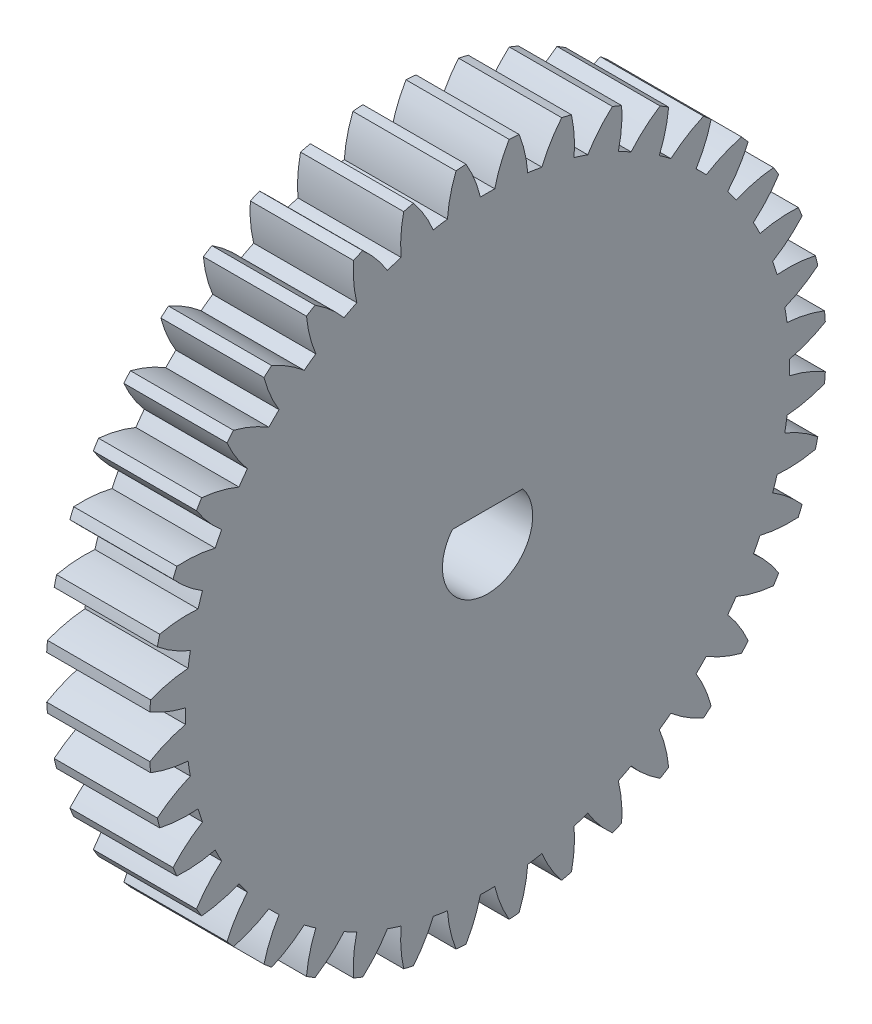
SolidWorks part; units mm, degrees
ref_plane "Plane1" through (0, 0, 0) normal (0, 0, 1) x (1, 0, 0)
ref_plane "Plane2" through (0, 0, 0) normal (0, 1, 0) x (1, 0, 0)
ref_plane "Plane3" through (0, 0, 0) normal (1, 0, 0) x (0, 0, -1)
sketch "HoldingSke" plane through (0, 0, 0) normal (0, 1, 0) x (1, 0, 0)
  line L0 (0, 0) -> (0.6128, -0.5142)
  line L1 (-15, 0) -> (100, 0) construction
  line L2 (0, 0) -> (-2.1039, 2.3779)
  line L3 (0, 0) -> (-11.863, 4.5341)
  line L4 (0, 0) -> (6.6156, 5.5511)
  line L5 (0, 0) -> (-46.8476, -17.4728)
  line L6 (0, 0) -> (-6.6317, -4.4744)
  line L7 (-2.1039, 2.3779) -> (8.6586, 51.2059)
  line L8 (-76.2, 54.61) -> (-75.2, 54.61)
  line L9 (-71.009, 38.7566) -> (-53.1078, 45.2721)
  line L10 (-76.2, 71.12) -> (104.1128, 71.12)
  line L11 (0, 0) -> (-8, 0)
  line L12 (-76.2, 101.6) -> (-76.155, 101.6)
  line L13 (24.9733, 27.94) -> (52.9518, 28.4284)
  line L14 (24.9733, 27.94) -> (24.9743, 27.94)
  line L15 (24.9733, 27.94) -> (100.4006, 29.5858)
  line L16 (-63.627, -1.25) -> (-12.827, -1.25)
  circle A0 centre (0, 0) radius 3.5
  circle A1 centre (0, 0) radius 23.4365
  circle A2 centre (0, 0) radius 37.5
  circle A3 centre (0, 0) radius 3.5
  dimension "MHD" = 46.873
  dimension "Hub_dia" = 75
  dimension "Bore" = 7
  dimension "MBD" = 7
  dimension "Num_teeth" = 40
  dimension "Pitch" = 0.8
  dimension "Overall_len" = 50
  dimension "Show_teeth" = 40
  dimension "Thickness" = 8
  dimension "OAL" = 50.0001
  dimension "T_dim" = 1
  dimension "Ap" = 20
  dimension "H" = 19.05
  dimension "Pitch_radius" = 180.3128
  dimension "Width" = 8
  dimension "Backlash" = 0.045
  dimension "Addendum_fac" = 1
  dimension "Dedendum_fac" = 1.25
  dimension "Clearance_fac" = 0.25
  dimension "Dedendum_add" = 0.001
  dimension "Module" = 1.25
sketch "BasProSke" plane through (0, 0, 0) normal (0, 1, 0) x (1, 0, 0)
  line L0 (-10, 0) -> (60, 0) construction
  line L1 (0, 0) -> (0, 26.25)
  line L2 (0, 0) -> (8, 0)
  line L3 (8, 0) -> (8, 26.25)
  line L4 (8, 26.25) -> (0, 26.25)
  dimension "Thickness" = 8
  dimension "Diameter" = 52.5
revolve "Base-Revolve" add sketch "BasProSke" angle 360 about L0
sketch "TooCutSke" plane through (0, 0, 0) normal (1, 0, 0) x (0, 0, -1)
  line L1 (0, 0) -> (0, 107) construction
  line L2 (0, 0) -> (-1.0602, 24.9775) construction
  line L3 (0, 0) -> (-3.9204, 49.8134) construction
  line L4 (-1.0602, 24.9775) -> (-1.9602, 24.9067) construction
  arc A0 (0.5568, 23.4299) -> (-0.5568, 23.4299) centre (0, 0) ccw
  arc A1 (1.6852, 26.2213) -> (-1.6852, 26.2213) centre (0, 0) ccw
  circle A2 centre (0, 0) radius 25 construction
  circle A3 centre (0, 0) radius 23.4923 construction
  arc A4 (-0.5568, 23.4299) -> (-1.6852, 26.2213) centre (-10.2865, 21.1205) ccw
  arc A5 (1.6852, 26.2213) -> (0.5568, 23.4299) centre (10.2865, 21.1205) ccw
  dimension "Root_dia" = 46.873
  dimension "Overcut_dia" = 52.5508
  dimension "Pitch_dia" = 50
  dimension "Base_dia" = 46.9846
  dimension "Flank_rad" = 10
  dimension "Half_ang" = 4.5
  dimension "Half_CT" = 0.9027
extrude "ToothCut" cut sketch "TooCutSke" along normal through all
fillet "Breaks" [suppressed] radius 0.025
fillet "RootFillets" [suppressed] radius 0.3135
pattern_circular "TeethCuts" count 40 every 9 about axis through (-10, 0, 0) along (1, 0, 0) of "ToothCut", "RootFillets", "Breaks"
sketch "HubNeaOneSke" plane through (0, 0, 0) normal (-1, 0, 0) x (0, 0, 1)
  circle A0 centre (0, 0) radius 23.4365
  dimension "Diameter" = 46.873
extrude "HubNearOne" [suppressed] add sketch "HubNeaOneSke" along normal blind 42.0001
sketch "HubNeaBotSke" plane through (0, 0, 0) normal (-1, 0, 0) x (0, 0, 1)
  circle A0 centre (0, 0) radius 23.4365
  dimension "Diameter" = 46.873
extrude "HubNearBoth" [suppressed] add sketch "HubNeaBotSke" along normal blind 21
ref_plane "FarPln" through (8, 0, 0) normal (1, 0, 0) x (0, 0, -1)
sketch "HubFarSke" plane through (8, 0, 0) normal (1, 0, 0) x (0, 0, -1)
  circle A0 centre (0, 0) radius 23.4365
  dimension "Diameter" = 46.873
extrude "HubFar" [suppressed] add sketch "HubFarSke" along normal blind 21
sketch "BorSke" plane through (0, 0, 0) normal (1, 0, 0) x (0, 0, -1)
  circle A0 centre (0, 0) radius 3.5
  dimension "Diameter" = 7
extrude "Bore" cut sketch "BorSke" along normal mid plane 100.0001
sketch "KeySke" plane through (0, 0, 0) normal (1, 0, 0) x (0, 0, -1)
  line L0 (-1, 0) -> (-1, 4.5)
  line L1 (-1, 4.5) -> (1, 4.5)
  line L2 (1, 4.5) -> (1, 0)
  line L3 (0, 0) -> (0, 34) construction
  line L4 (-1, 0) -> (1, 0)
  dimension "Offset" = 4.5
  dimension "Width" = 2
extrude "Keyway" [suppressed] cut sketch "KeySke" along normal mid plane 100.0001
pattern_circular "Keyway2" [suppressed] count 2 every 90 about axis through (-10, 0, 0) along (1, 0, 0)
sketch "Sketch1" plane through (8, 0, 0) normal (1, 0, 0) x (0, 0, -1)
  line L0 (-2.7305, 2.1896) -> (2.7305, 2.1896)
  circle A0 centre (0, 0) radius 3.5 construction
  circle A1 centre (0, 0) radius 3.5
  point P5 (0, -3.5)
  dimension "D1" = 5.6896
extrude "Boss-Extrude1" add sketch "Sketch1" against normal up to surface (8 mm away) contours L0 A1
equation "' \"Module@HoldingSke\" = 6.35"
equation "' \"Num_teeth@HoldingSke\" = 12"
equation "' \"Ap@HoldingSke\" =  20"
equation "' \"Ap@HoldingSke\" = 20"
equation "' \"Width@HoldingSke\" = 0.5 * 25.4"
equation "' \"Hub_dia@HoldingSke\"= 1 * 25.4"
equation "' \"Hub_dia@HoldingSke\" = 1 * 25.4"
equation "' \"Overall_len@HoldingSke\" = 1.0 * 25.4"
equation "' \"Bore@HoldingSke\" = 0.75 * 25.4"
equation "' \"T_dim@HoldingSke\" = 0.1 * 25.4"
equation "' \"Width@KeySke\" = 0.25 * 25.4"
equation "' \"Show_teeth@HoldingSke\" = 13"
equation "' \"Backlash@HoldingSke\" = 0.009 * 25.4"
equation "' \"Addendum_fac@HoldingSke\" = 1.0"
equation "' \"Dedendum_fac@HoldingSke\" = 1.25"
equation "' \"Dedendum_add@HoldingSke\" = 0.00005 * 25.4"
equation "' \"Clearance_fac@HoldingSke\" = 0.25"
equation "\"Pitch@HoldingSke\" = 1 / \"Module@HoldingSke\""
equation "\"Overcut_dia@TooCutSke\" = (\"Num_teeth@HoldingSke\" + 2 * \"Addendum_fac@HoldingSke\") / \"Pitch@HoldingSke\" + 0.002 * 25.4"
equation "\"Pitch_dia@TooCutSke\" = \"Num_teeth@HoldingSke\" / \"Pitch@HoldingSke\""
equation "\"Base_dia@TooCutSke\" = \"Num_teeth@HoldingSke\" / \"Pitch@HoldingSke\" * cos((\"Ap@HoldingSke\"  * 3.14159265 / 180))"
equation "\"Root_dia@TooCutSke\" = (\"Num_teeth@HoldingSke\" + 2) / \"Pitch@HoldingSke\" - 2 * (\"Addendum_fac@HoldingSke\" + \"Dedendum_fac@HoldingSke\") / \"Pitch@HoldingSke\" - \"Dedendum_add@HoldingSke\" * 2"
equation "\"Half_ang@TooCutSke\" = 180 / \"Num_teeth@HoldingSke\""
equation "\"Half_CT@TooCutSke\" = \"Num_teeth@HoldingSke\" / \"Pitch@HoldingSke\" * sin((3.14159265 / 2 / \"Num_teeth@HoldingSke\")) / 2 - 7 * \"Backlash@HoldingSke\" / 4"
equation "\"Flank_rad@TooCutSke\" = \"Num_teeth@HoldingSke\" / \"Pitch@HoldingSke\" / 5"
equation "\"Radius@RootFillets\" = \"Clearance_fac@HoldingSke\" / \"Pitch@HoldingSke\" + \"Dedendum_add@HoldingSke\""
equation "\"Break_rad@Breaks\" = 0.02 / \"Pitch@HoldingSke\""
equation "\"Thickness@HoldingSke\" = \"Width@HoldingSke\""
equation "\"OAL@HoldingSke\" = \"Thickness@HoldingSke\""
equation "\"MHD@HoldingSke\" = (\"Num_teeth@HoldingSke\" + 2) / \"Pitch@HoldingSke\" - 2 * (\"Addendum_fac@HoldingSke\" + \"Dedendum_fac@HoldingSke\")  / \"Pitch@HoldingSke\" - \"Dedendum_add@HoldingSke\" * 2"
equation "\"MBD@HoldingSke\" = (\"Num_teeth@HoldingSke\" + 2) / \"Pitch@HoldingSke\" - 2 * (\"Addendum_fac@HoldingSke\" + \"Dedendum_fac@HoldingSke\")  / \"Pitch@HoldingSke\" - \"Dedendum_add@HoldingSke\" * 2 - 0.002 * 25.4"
equation "\"MHD@HoldingSke\" = ((sgn( \"MHD@HoldingSke\" - \"Hub_dia@HoldingSke\" )-1)*( \"MHD@HoldingSke\" - \"Hub_dia@HoldingSke\" ))/-2+ \"Hub_dia@HoldingSke\""
equation "\"MBD@HoldingSke\" = ((sgn( \"MBD@HoldingSke\" - \"Bore@HoldingSke\" )-1)*( \"MBD@HoldingSke\" - \"Bore@HoldingSke\" ))/-2+ \"Bore@HoldingSke\""
equation "\"OAL@HoldingSke\" = ((sgn( \"OAL@HoldingSke\" - \"Overall_len@HoldingSke\" )+1)*( \"OAL@HoldingSke\" - \"Overall_len@HoldingSke\" ))/2 + \"Overall_len@HoldingSke\" + 0.000002 * 25.4"
equation "\"Num_teeth@TeethCuts\" = int( \"Show_teeth@HoldingSke\" ) + 1"
equation "\"Num_teeth@TeethCuts\" = ((sgn( \"Num_teeth@TeethCuts\" - \"Num_teeth@HoldingSke\" )-1)*( \"Num_teeth@TeethCuts\" - \"Num_teeth@HoldingSke\" ))/-2+ \"Num_teeth@HoldingSke\""
equation "\"Num_teeth@TeethCuts\" = ((sgn( \"Num_teeth@TeethCuts\" - 2.0)+1)*( \"Num_teeth@TeethCuts\" - 2.0))/2 +2.0"
equation "\"Angle@TeethCuts\" = 360.0 / \"Num_teeth@HoldingSke\""
equation "\"Diameter@BasProSke\" = (\"Num_teeth@HoldingSke\" + 2 * \"Addendum_fac@HoldingSke\") / \"Pitch@HoldingSke\""
equation "\"Thickness@BasProSke\"  = \"Thickness@HoldingSke\""
equation "' \"Fillet_rad@BasProSke\" =  \"Thickness@HoldingSke\" * 0.05"
equation "' \"Fillet_rad@BasProSke\" = \"Thickness@HoldingSke\" * 0.05"
equation "\"MHD@HoldingSke\" = ((sgn( \"MHD@HoldingSke\" - \"Root_dia@TooCutSke\" )-1)*( \"MHD@HoldingSke\" - \"Root_dia@TooCutSke\" ))/-2+ \"Root_dia@TooCutSke\""
equation "\"Diameter@HubNeaOneSke\" = \"MHD@HoldingSke\""
equation "\"Length@HubNearOne\" = \"OAL@HoldingSke\" - \"Thickness@BasProSke\""
equation "\"Diameter@HubNeaBotSke\" = \"MHD@HoldingSke\""
equation "\"Length@HubNearBoth\" = ( \"OAL@HoldingSke\" - \"Thickness@BasProSke\" ) / 2.0"
equation "\"Thickness@FarPln\" = \"Thickness@BasProSke\""
equation "\"Diameter@HubFarSke\" = \"MHD@HoldingSke\""
equation "\"Length@HubFar\" = ( \"OAL@HoldingSke\" - \"Thickness@BasProSke\" ) / 2.0"
equation "\"Diameter@BorSke\" = \"MBD@HoldingSke\""
equation "\"D1@Bore\" = \"OAL@HoldingSke\" * 2.0"
equation "\"D1@Keyway\" = \"OAL@HoldingSke\" * 2.0"
equation "\"Offset@KeySke\" = \"T_dim@HoldingSke\" + \"MBD@HoldingSke\" / 2.0"
